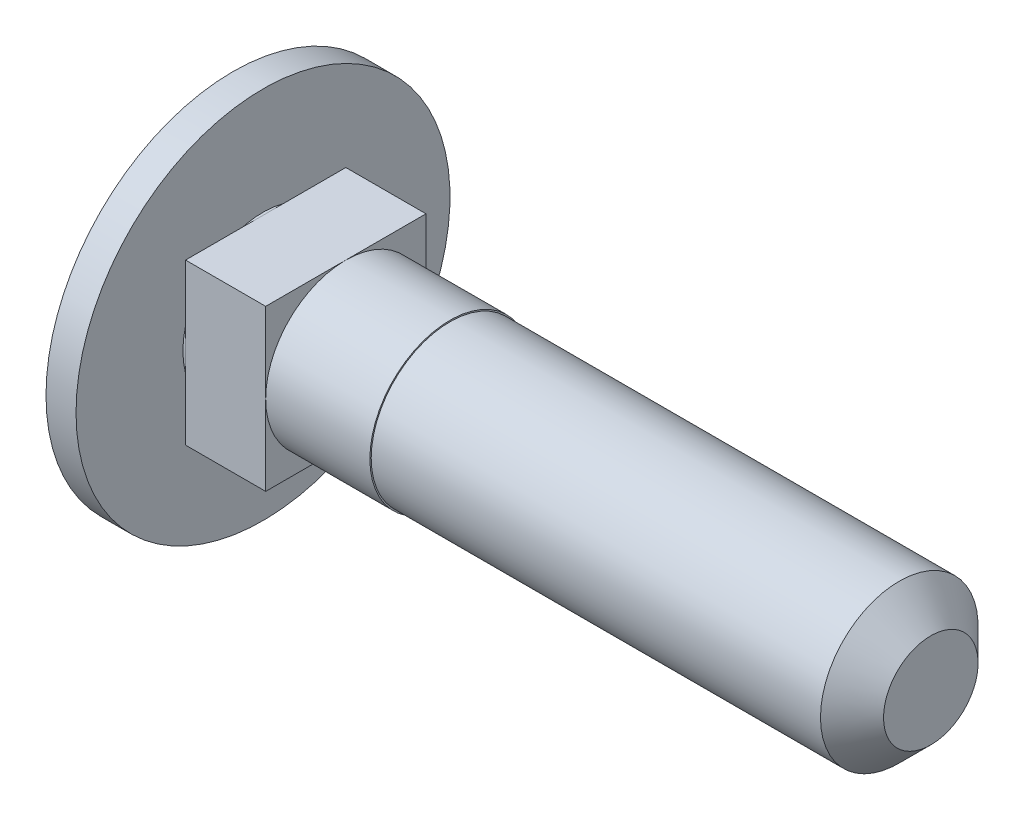
SolidWorks part; units mm, degrees
material "Серое литое железо"
ref_plane "Спереди" through (0, 0, 0) normal (0, 0, 1) x (1, 0, 0)
ref_plane "Сверху" through (0, 0, 0) normal (0, 1, 0) x (1, 0, 0)
ref_plane "Справа" through (0, 0, 0) normal (1, 0, 0) x (0, 0, -1)
sketch "Эскиз1" plane through (0, 0, 0) normal (0, 0, 1) x (1, 0, 0)
  line L0 (-121.4305, 0) -> (5950.0947, 0) construction
  line L1 (25, 0) -> (25, 2.95)
  line L2 (25, 2.95) -> (7, 2.95)
  line L3 (7, 2.95) -> (7, 3)
  line L4 (7, 3) -> (0, 3)
  line L5 (0, 3) -> (0, 7)
  line L6 (0, 7) -> (-1.1244, 7)
  line L7 (25, 0) -> (-3, 0)
  arc A0 (-1.1244, 7) -> (-3, 0) centre (11, 0) ccw
  point P13 (25, 1.475)
  dimension "R" = 14
  dimension "d" = 6
  dimension "D1" = 5.9
  dimension "d_D" = 14
  dimension "k" = 3
  dimension "b" = 18
  dimension "l" = 25
revolve "Повернуть1" add sketch "Эскиз1" angle 360 about L0
sketch "Эскиз2" plane through (0, 0, 0) normal (1, 0, 0) x (0, 0, -1)
  line L1 (-3, 3) -> (3, 3)
  line L2 (-3, 3) -> (-3, -3)
  line L3 (-3, -3) -> (3, -3)
  line L4 (3, 3) -> (3, -3)
  line L5 (-3, 3) -> (3, -3) construction
  line L6 (-3, -3) -> (3, 3) construction
  circle A0 centre (0, 0) radius 3 construction
  circle A1 centre (0, 0) radius 3 construction
  circle A2 centre (0, 0) radius 3 construction
  point P0 (0, 0)
extrude "Бобышка-Вытянуть1" add sketch "Эскиз2" along normal blind 3 from offset 0.1
chamfer "Фаска1" distance 1.18 1 edges at (25, 0, 2.95)
equation "\"D1@Эскиз1\"=\"d@Эскиз1\"-0.1"
equation "\"D1@Фаска1\"= \"D1@Эскиз1\" / 5"
